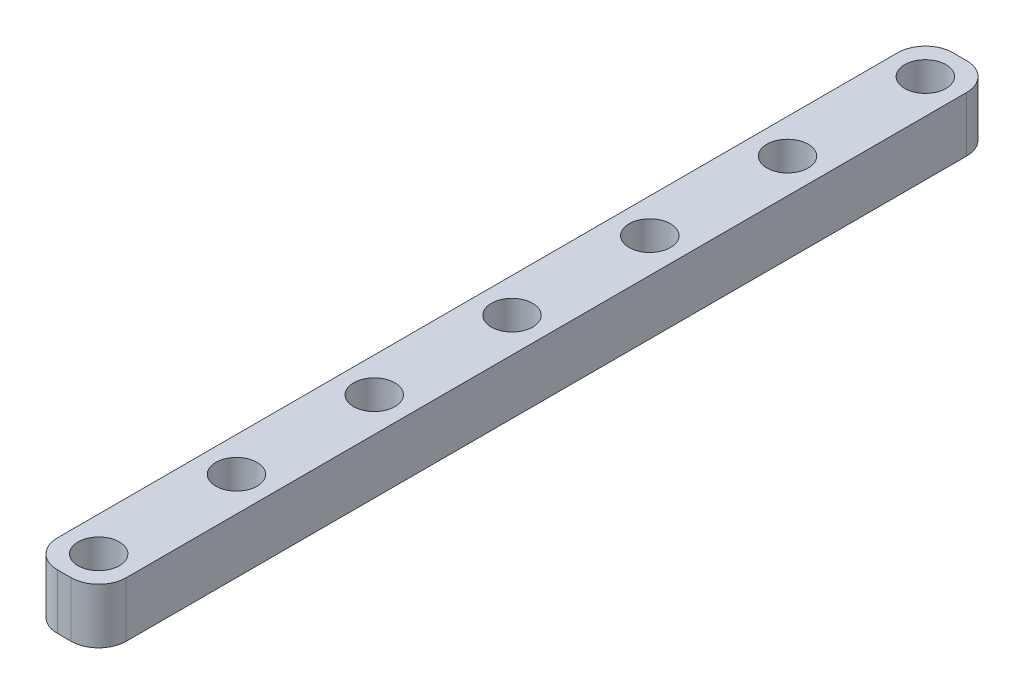
SolidWorks part; units mm, degrees
ref_plane "Front Plane" through (0, 0, 0) normal (0, 0, 1) x (1, 0, 0)
ref_plane "Top Plane" through (0, 0, 0) normal (0, 1, 0) x (1, 0, 0)
ref_plane "Right Plane" through (0, 0, 0) normal (1, 0, 0) x (0, 0, -1)
sketch "Sketch2" plane through (0, 0, 0) normal (0, 1, 0) x (1, 0, 0)
  line L1 (0, 0) -> (-5, 0)
  line L2 (0, 0) -> (0, 65)
  line L3 (0, 65) -> (-5, 65)
  line L4 (-5, 0) -> (-5, 65)
  point P5 (-2.5, 0)
  dimension "D1" = 5
  dimension "D2" = 65
extrude "Boss-Extrude1" add sketch "Sketch2" along normal blind 4 contours L4 L3 L2 L1
sketch "Sketch3" plane through (0, 4, 0) normal (0, 1, 0) x (1, 0, 0)
  line L0 (-2.5, 65) -> (-2.5, 0) construction
  line L1 (0, 65) -> (-5, 65) construction
  line L2 (0, 0) -> (-5, 0) construction
  line L3 (-5, 32.5) -> (0, 32.5) construction
  line L4 (-5, 0) -> (-5, 65) construction
  line L5 (0, 0) -> (0, 65) construction
  circle A0 centre (-2.5, 32.5) radius 1.5
  circle A1 centre (-2.5, 22.5) radius 1.5
  circle A2 centre (-2.5, 12.5) radius 1.5
  circle A3 centre (-2.5, 2.5) radius 1.5
  circle A4 centre (-2.5, 42.5) radius 1.5
  circle A5 centre (-2.5, 52.5) radius 1.5
  circle A6 centre (-2.5, 62.5) radius 1.5
  point P15 (-2.5, 32.5)
  dimension "D1" = 3
  dimension "D2" = 4
  dimension "D3" = 4
extrude "Cut-Extrude1" cut sketch "Sketch3" against normal blind 4
fillet "Fillet2" radius 2 4 edges at (0, 2, -65) (-5, 2, -65) (-5, 2, 0) (0, 2, 0)
